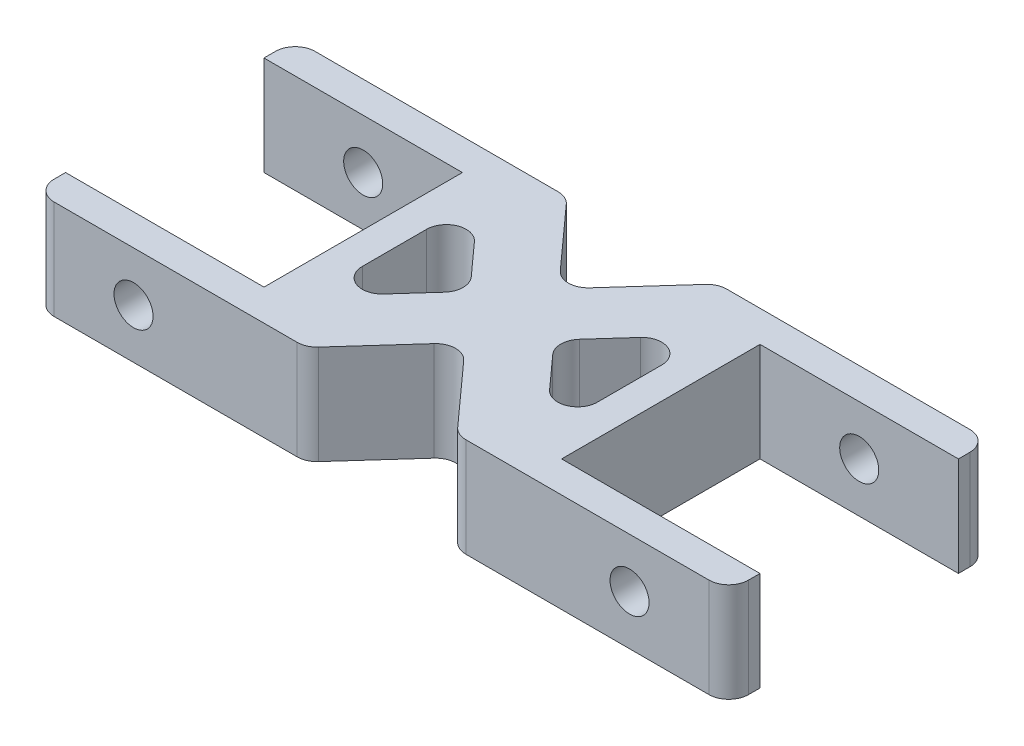
SolidWorks part; units mm, degrees
material "ABS"
ref_plane "Front Plane" through (0, 0, 0) normal (0, 0, 1) x (1, 0, 0)
ref_plane "Top Plane" through (0, 0, 0) normal (0, 1, 0) x (1, 0, 0)
ref_plane "Right Plane" through (0, 0, 0) normal (1, 0, 0) x (0, 0, -1)
sketch "Sketch1" plane through (0, 0, 0) normal (0, 1, 0) x (1, 0, 0)
  line L0 (19.05, 0) -> (-19.05, 0) construction
  line L1 (-19.05, -12.7) -> (-19.05, 12.7)
  line L2 (19.05, -12.7) -> (19.05, 12.7)
  line L3 (-19.05, 12.7) -> (-44.45, 12.7)
  line L4 (-44.45, -12.7) -> (-19.05, -12.7)
  line L5 (19.05, 12.7) -> (44.45, 12.7)
  line L6 (19.05, -12.7) -> (44.45, -12.7)
  line L7 (-44.45, -16.7) -> (-9.6653, -16.7)
  line L8 (-15.05, -10.725) -> (-15.05, 10.725)
  line L9 (-9.6653, 16.7) -> (-44.45, 16.7)
  line L10 (-44.45, 16.7) -> (-44.45, 12.7)
  line L11 (9.6653, -16.7) -> (44.45, -16.7)
  line L12 (15.05, -10.725) -> (15.05, 10.725)
  line L13 (9.6653, 16.7) -> (44.45, 16.7)
  line L14 (44.45, -16.7) -> (44.45, -12.7)
  line L15 (-44.45, -12.7) -> (-44.45, -16.7)
  line L16 (44.45, 12.7) -> (44.45, 16.7)
  line L17 (-15.05, -16.7) -> (15.05, 16.7) construction
  line L18 (15.05, -16.7) -> (-15.05, 16.7) construction
  line L19 (9.6653, -16.7) -> (0, -5.975)
  line L20 (-15.05, -10.725) -> (-5.3847, 0)
  line L21 (15.05, -10.725) -> (5.3847, 0)
  line L22 (-9.6653, -16.7) -> (0, -5.975)
  line L23 (-15.05, 16.7) -> (-44.45, 16.7) construction
  line L24 (15.05, 16.7) -> (44.45, 16.7) construction
  line L25 (15.05, -16.7) -> (44.45, -16.7) construction
  line L26 (-44.45, -16.7) -> (-15.05, -16.7) construction
  line L27 (-12.0786, -19.3778) -> (18.0214, 14.0222) construction
  line L28 (-18.0214, -14.0222) -> (12.0786, 19.3778) construction
  line L29 (-15.05, -16.7) -> (-15.05, 16.7) construction
  line L30 (12.0786, -19.3778) -> (-18.0214, 14.0222) construction
  line L31 (18.0214, -14.0222) -> (-12.0786, 19.3778) construction
  line L32 (15.05, -16.7) -> (15.05, 16.7) construction
  line L33 (-5.3847, 0) -> (-15.05, 10.725)
  line L34 (5.3847, 0) -> (15.05, 10.725)
  line L35 (0, 5.975) -> (-9.6653, 16.7)
  line L36 (0, 5.975) -> (9.6653, 16.7)
  point P4 (0, 0)
  point P7 (-19.05, 0)
  point P10 (19.05, 0)
  dimension "D1" = 38.1
  dimension "D2" = 25.4
  dimension "D3" = 25.4
  dimension "D4" = 4
  dimension "D5" = 4
  dimension "D6" = 4
  dimension "D7" = 4
extrude "Boss-Extrude1" add sketch "Sketch1" along normal blind 12.7
fillet "Fillet1" radius 2.54 16 edges at (15.05, 6.35, -10.725) (5.3847, 6.35, 0) (15.05, 6.35, 10.725) (-15.05, 6.35, -10.725) (-15.05, 6.35, 10.725) (-5.3847, 6.35, 0) (-44.45, 6.35, -16.7) (9.6653, 6.35, -16.7) (44.45, 6.35, -16.7) (44.45, 6.35, 16.7) (9.6653, 6.35, 16.7) (0, 6.35, 5.975) (-9.6653, 6.35, 16.7) (-44.45, 6.35, 16.7) (0, 6.35, -5.975) (-9.6653, 6.35, -16.7)
sketch "Sketch3" plane through (0, 0, -12.7) normal (0, 0, 1) x (1, 0, 0)
  line L0 (-44.45, 12.7) -> (-19.05, 12.7) construction
  line L1 (-19.05, 12.7) -> (-19.05, 0) construction
  line L2 (19.05, 12.7) -> (44.45, 12.7) construction
  line L3 (44.45, 12.7) -> (44.45, 0) construction
  circle A0 centre (-31.75, 6.35) radius 2.5
  circle A1 centre (31.75, 6.35) radius 2.5
  point P0 (-31.75, 12.7)
  point P1 (-19.05, 6.35)
  point P8 (31.75, 12.7)
  point P9 (44.45, 6.35)
  dimension "D1" = 5
  dimension "D2" = 5
extrude "Cut-Extrude1" cut sketch "Sketch3" against normal through all both and the other way through all
